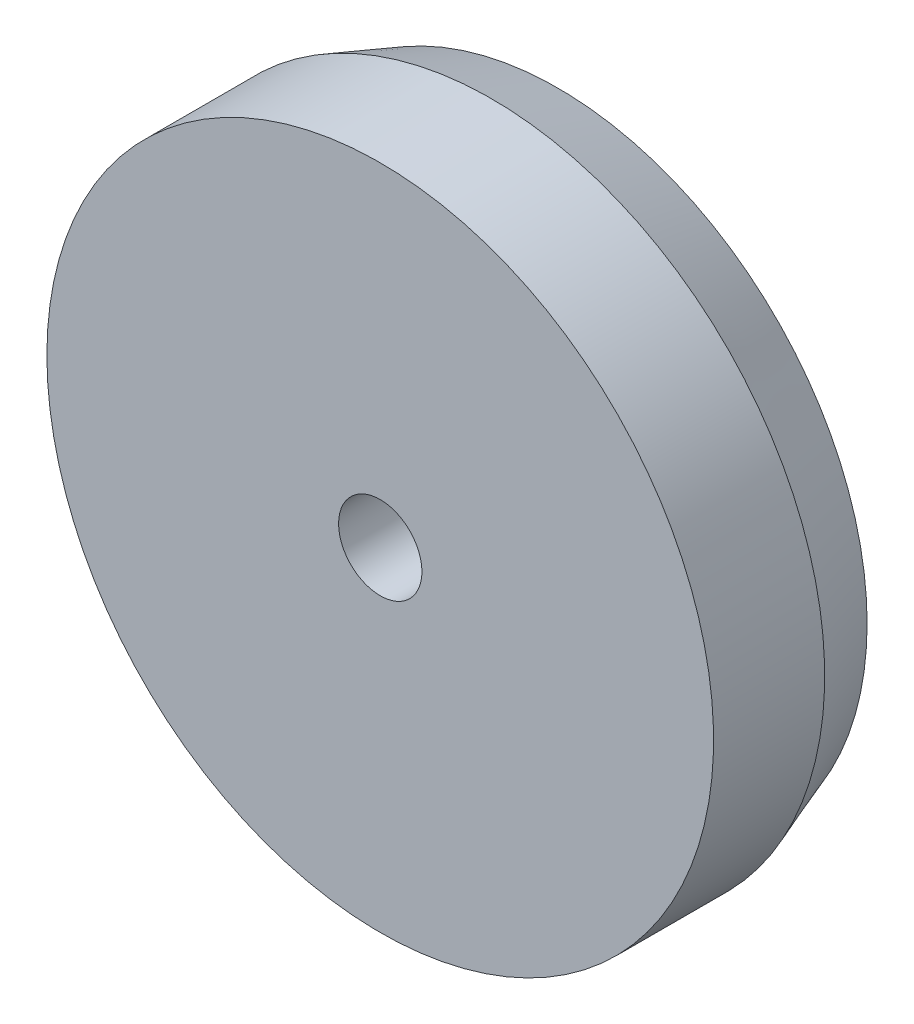
SolidWorks part; units mm, degrees
ref_plane "Alzado" through (0, 0, 0) normal (0, 0, 1) x (1, 0, 0)
ref_plane "Planta" through (0, 0, 0) normal (0, 1, 0) x (1, 0, 0)
ref_plane "Vista lateral" through (0, 0, 0) normal (1, 0, 0) x (0, 0, -1)
ref_plane "Plane1" through (0, -10.646, 0) normal (0, -1, 0) x (1, 0, 0)
sketch "Sketch1" plane through (0, -10.646, 0) normal (0, -1, 0) x (1, 0, 0)
  line L0 (5.297, -1.87) -> (5.297, -1.67)
  line L1 (5.297, -1.67) -> (4.772, -1.67)
  line L2 (4.772, -1.67) -> (4.772, -1.87)
  line L3 (5.147, -1.99) -> (5.2533, -1.99)
  line L4 (5.2533, -1.99) -> (5.297, -1.87)
  line L5 (4.697, -1.67) -> (4.697, -1.99) construction
  arc A0 (4.772, -1.87) -> (5.147, -1.99) centre (4.697, -2.7503) cw
  dimension "D1" = 0.8835
  dimension "D2" = 0.075
  dimension "D3" = 0.45
  dimension "D4" = 0.5563
  dimension "D5" = 0.6
  dimension "D6" = 0.2
revolve "Revolve1" add sketch "Sketch1" angle 360 about L5
